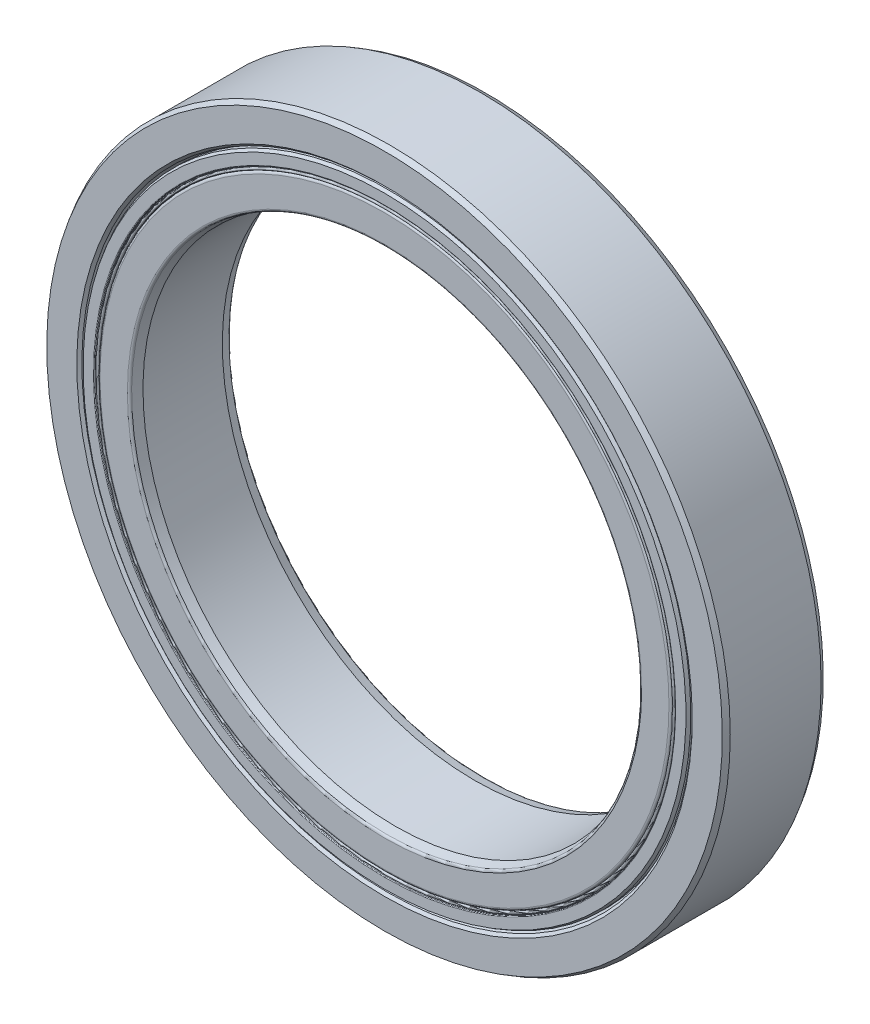
SolidWorks part; units mm, degrees
ref_plane "Front Plane" through (0, 0, 0) normal (0, 0, 1) x (1, 0, 0)
ref_plane "Top Plane" through (0, 0, 0) normal (0, 1, 0) x (1, 0, 0)
ref_plane "Right Plane" through (0, 0, 0) normal (1, 0, 0) x (0, 0, -1)
sketch "Sketch1" plane through (0, 0, 0) normal (0, 0, 1) x (1, 0, 0)
  line L0 (-13.5, 0) -> (13.5, 0) construction
  line L1 (-10, 0) -> (10, 0) construction
  circle A0 centre (0, 0) radius 10 construction
  circle A1 centre (0, 0) radius 13.5 construction
  point P3 (0, 0)
  point P6 (0, 0)
  point P7 (0, -10)
  point P11 (0, -13.5)
  point P12 (0, 10)
  point P13 (0, 13.5)
  dimension "OD" = 27
  dimension "ID" = 20
sketch "Sketch2" plane through (0, 0, 0) normal (1, 0, 0) x (0, 0, -1)
  line L0 (-2, 13.5) -> (2, 13.5) construction
  line L1 (0, 13.5) -> (0, -13.5) construction
  line L2 (1.8, 13.5) -> (-1.8, 13.5)
  line L3 (-1.8, 13.5) -> (-2, 13.3845)
  line L4 (-2, 13.3845) -> (-2, 12.194)
  line L5 (-1.683, 12.015) -> (-1.2723, 12.015)
  line L6 (1.683, 12.015) -> (1.2723, 12.015)
  line L7 (2, 13.3845) -> (2, 12.194)
  line L8 (1.8, 13.5) -> (2, 13.3845)
  line L9 (-1.2723, 12.015) -> (-1.2723, 12.51) construction
  line L10 (-1.2723, 12.51) -> (-1.2723, 13.005) construction
  line L11 (0, 13.5) -> (0, -13.5) construction
  line L12 (-2, 0) -> (2, 0) construction
  line L13 (2, 10) -> (-2, 10) construction
  line L14 (-2, 10) -> (-2, -10) construction
  line L15 (-2, -10) -> (2, -10) construction
  line L16 (2, 13.5) -> (2, -13.5) construction
  line L17 (-1.2723, 13.005) -> (-1.2723, 13.5) construction
  line L18 (-1.2723, 13.005) -> (0, 13.005) construction
  line L20 (-1.683, 12.015) -> (-1.9, 12.094)
  line L21 (-1.9, 12.094) -> (-2, 12.194)
  line L26 (1.9, 12.094) -> (2, 12.194)
  line L27 (1.683, 12.015) -> (1.9, 12.094)
  arc A0 (-1.2723, 12.015) -> (1.2723, 12.015) centre (0, 11.6925) cw
  circle A1 centre (0, 11.6925) radius 1.3125 construction
  point P17 (0, 0)
  point P21 (0, 13.5)
  point P30 (0, -10)
  dimension "Approx. Ball Dia." = 2.625
  dimension "Width" = 4
  dimension "For Shaft Diameter" = 20
  dimension "For Housing ID" = 27
  dimension "D4" = 24.03
  dimension "D2" = 20
  dimension "D5" = 45
  dimension "D1" = 30
  dimension "D6" = 0.2
  dimension "D7" = 0.1
sketch "Sketch3" plane through (0, 0, 0) normal (1, 0, 0) x (0, 0, -1)
  line L14 (-1.683, 12.015) -> (-1.9, 12.094) construction
  line L15 (-1.9, 12.094) -> (-2, 12.194) construction
  line L16 (-2, 13.3845) -> (-2, 12.194) construction
  line L17 (-1.8, 13.5) -> (-2, 13.3845) construction
  line L18 (1.8, 13.5) -> (-1.8, 13.5) construction
  line L19 (1.8, 13.5) -> (2, 13.3845) construction
  line L20 (2, 13.3845) -> (2, 12.194) construction
  line L21 (1.9, 12.094) -> (2, 12.194) construction
  line L22 (1.683, 12.015) -> (1.9, 12.094) construction
  line L23 (1.683, 12.015) -> (1.2723, 12.015) construction
  line L24 (-1.683, 12.015) -> (-1.2723, 12.015) construction
  line L25 (-1.683, 12.015) -> (-1.9, 12.094)
  line L26 (-1.9, 12.094) -> (-2, 12.194)
  line L27 (-2, 13.3845) -> (-2, 12.194)
  line L28 (-1.8, 13.5) -> (-2, 13.3845)
  line L29 (1.8, 13.5) -> (-1.8, 13.5)
  line L30 (1.8, 13.5) -> (2, 13.3845)
  line L31 (2, 13.3845) -> (2, 12.194)
  line L32 (1.9, 12.094) -> (2, 12.194)
  line L33 (1.683, 12.015) -> (1.9, 12.094)
  line L34 (1.683, 12.015) -> (1.2723, 12.015)
  line L35 (-1.683, 12.015) -> (-1.2723, 12.015)
  arc A2 (1.2723, 12.015) -> (-1.2723, 12.015) centre (0, 11.6925) ccw construction
  arc A3 (1.2723, 12.015) -> (-1.2723, 12.015) centre (0, 11.6925) ccw
revolve "Revolve1" add sketch "Sketch3" angle 360 about L12
sketch "Sketch4" plane through (0, 0, 0) normal (1, 0, 0) x (0, 0, -1)
  line L0 (0, 13.5) -> (0, -13.5) construction
  line L1 (0, 13.5) -> (0, -13.5) construction
  line L2 (-1.5726, 10) -> (-1.9271, 10.095)
  line L3 (-2, 10.19) -> (-2, 11.2716)
  line L4 (2, -13.3845) -> (2, 13.3845) construction
  line L5 (-1.9016, 11.37) -> (-1.2723, 11.37)
  line L6 (-1.5726, 10) -> (1.5726, 10)
  line L7 (2, 13.3845) -> (2, 12.194) construction
  line L8 (1.5726, 10) -> (1.9271, 10.095)
  line L9 (0, 13.005) -> (0, 10) construction
  line L10 (2, 10.19) -> (2, 11.2716)
  line L11 (1.9016, 11.37) -> (1.2723, 11.37)
  line L12 (1.5726, 10) -> (1.5726, 10.095) construction
  line L13 (1.5726, 10.095) -> (1.5726, 10.19) construction
  line L14 (1.5726, 10.19) -> (1.5726, 10.285) construction
  line L15 (1.5726, 10.285) -> (1.5726, 10.38) construction
  circle A0 centre (0, 11.6925) radius 1.3125 construction
  arc A1 (1.2723, 11.37) -> (-1.2723, 11.37) centre (0, 11.6925) cw
  arc A2 (2, 11.2716) -> (1.9016, 11.37) centre (1.9016, 11.2716) ccw
  arc A3 (-2, 11.2716) -> (-1.9016, 11.37) centre (-1.9016, 11.2716) cw
  arc A4 (1.9271, 10.095) -> (2, 10.19) centre (1.9016, 10.19) ccw
  arc A5 (-1.9271, 10.095) -> (-2, 10.19) centre (-1.9016, 10.19) cw
  point P14 (2, 10.1145)
  point P36 (0, 10.38)
  dimension "D1" = 15
revolve "Revolve2" add sketch "Sketch4" angle 360 about L12
sketch "Sketch5" plane through (0, 0, 0) normal (1, 0, 0) x (0, 0, -1)
  line L0 (-1.3125, 11.6925) -> (1.3125, 11.6925)
  arc A2 (-1.3125, 11.6925) -> (1.3125, 11.6925) centre (0, 11.6925) cw
  arc A3 (1.2723, 12.015) -> (-1.2723, 12.015) centre (0, 11.6925) ccw construction
revolve "Revolve3" add sketch "Sketch5" angle 360 about L0
pattern_circular "CirPattern1" count 18 over 360 about axis through (0, 0, 0) along (0, 0, 1) of bodies 104
sketch "Sketch6" plane through (0, 0, 0) normal (1, 0, 0) x (0, 0, -1)
  line L1 (-1.8788, 12.015) -> (-1.3125, 12.015)
  line L2 (-2, 11.945) -> (-2, 11.538)
  line L3 (-1.972, 11.51) -> (-1.3125, 11.51)
  line L4 (-1.3125, 12.015) -> (-1.3125, 11.51)
  line L5 (-2, 10.19) -> (-2, 11.2716) construction
  line L6 (-1.8, 13.5) -> (-2, 13.3845) construction
  line L7 (0, 13.5) -> (0, 10) construction
  line L8 (1.972, 11.51) -> (1.3125, 11.51)
  line L9 (1.3125, 12.015) -> (1.3125, 11.51)
  line L10 (1.8788, 12.015) -> (1.3125, 12.015)
  line L11 (2, 11.945) -> (2, 11.538)
  line L13 (-1.9016, 11.37) -> (-1.2723, 11.37) construction
  line L14 (-2, 11.945) -> (-1.8788, 12.015)
  line L15 (-1.683, 12.015) -> (-1.2723, 12.015) construction
  line L16 (2, 11.945) -> (1.8788, 12.015)
  arc A0 (-2, 11.538) -> (-1.972, 11.51) centre (-1.972, 11.538) ccw
  circle A1 centre (0, 11.6925) radius 1.3125 construction
  arc A2 (2, 11.538) -> (1.972, 11.51) centre (1.972, 11.538) cw
  point P26 (-2, 11.51)
  dimension "D3" = 0.028
  dimension "D1" = 0.14
  dimension "D2" = 0.07
revolve "Revolve4" add sketch "Sketch6" angle 360 about L12
sketch "Sketch7" plane through (0, 0, 0) normal (1, 0, 0) x (0, 0, -1)
  line L3 (-1.3125, 11.51) -> (-1.8906, 11.51)
  line L4 (-1.972, 11.51) -> (-1.3125, 11.51) construction
  line L7 (0, 10.38) -> (0, 10) construction
  line L8 (0, 13.5) -> (0, -13.5) construction
  line L21 (-1.8906, 11.51) -> (-1.925, 11.5039)
  line L22 (-1.9225, 11.475) -> (-1.9475, 11.475)
  line L23 (-1.9475, 11.37) -> (-1.3125, 11.37)
  line L24 (-1.3125, 11.37) -> (-1.3125, 11.51)
  line L25 (-1.9016, 11.37) -> (-1.2723, 11.37) construction
  line L26 (-2, 11.538) -> (-2, 11.37) construction
  line L27 (-2, 11.37) -> (-1.9475, 11.37) construction
  line L28 (-1.8906, 11.51) -> (-1.8906, 11.475) construction
  line L29 (-1.8906, 11.475) -> (-1.8906, 11.44) construction
  line L30 (-1.8906, 11.44) -> (-1.8906, 11.405) construction
  line L31 (-1.8906, 11.405) -> (-1.8906, 11.37) construction
  circle A2 centre (0, 11.6925) radius 1.3125 construction
  arc A9 (-1.925, 11.5039) -> (-1.9225, 11.475) centre (-1.9225, 11.4896) ccw
  arc A10 (-1.9475, 11.475) -> (-1.9475, 11.37) centre (-1.9475, 11.4225) ccw
  dimension "D1" = 0.025
  dimension "D2" = 10
revolve "Revolve5" add sketch "Sketch7" angle 360 about L12
equation "\"D4@Sketch2\"=\"OD@Sketch1\"*.89"
equation "\"D1@Sketch6\"=(\"OD@Sketch1\"-\"ID@Sketch1\")*.02"
equation "\"D2@Sketch6\"=\"D1@Sketch6\"*.5"
equation "\"D3@Sketch6\"=\"D1@Sketch6\"*.2"
equation "\"D6@Sketch2\"=\"Width@Sketch2\"*.05"
equation "\"D7@Sketch2\"=\"D6@Sketch2\"*.5"
equation "\"D1@CirPattern1\" =  ( pi * \"OD@Sketch1\" )  * .5625 / \"Approx. Ball Dia.@Sketch2\""
equation "\"Approx. Ball Dia.@Sketch2\"=(\"OD@Sketch1\"-\"ID@Sketch1\")*.5*.75"
